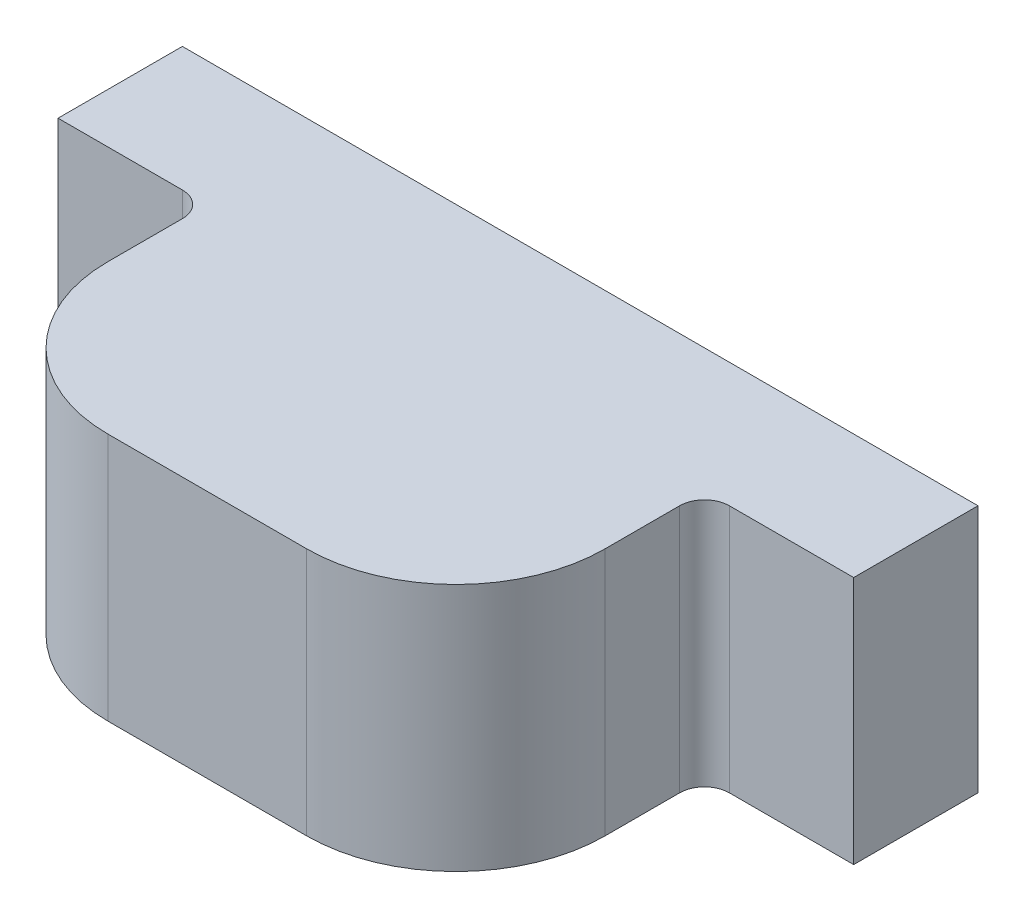
SolidWorks part; units mm, degrees
ref_plane "Front Plane" through (0, 0, 0) normal (0, 0, 1) x (1, 0, 0)
ref_plane "Top Plane" through (0, 0, 0) normal (0, 1, 0) x (1, 0, 0)
ref_plane "Right Plane" through (0, 0, 0) normal (1, 0, 0) x (0, 0, -1)
sketch "Sketch1" plane through (0, 0, 0) normal (0, 1, 0) x (1, 0, 0)
  line L0 (-1.1, -0.25) -> (-1.6, -0.25)
  line L1 (1.6, 0.25) -> (-1.6, 0.25)
  line L2 (1.6, 0.25) -> (1.6, -0.25)
  line L3 (1.6, -0.25) -> (1.1, -0.25)
  line L4 (-1.6, 0.25) -> (-1.6, -0.25)
  line L5 (1.6, 0.25) -> (-1.6, -0.25) construction
  line L6 (1.6, -0.25) -> (-1.6, 0.25) construction
  line L7 (0.4, -1.25) -> (-0.4, -1.25)
  line L8 (1, -0.65) -> (1, -0.35)
  line L10 (-1, -0.65) -> (-1, -0.35)
  line L11 (1, -1.25) -> (-1, -0.25) construction
  line L12 (1, -0.25) -> (-1, -1.25) construction
  arc A0 (0.4, -1.25) -> (1, -0.65) centre (0.4, -0.65) ccw
  arc A1 (-0.4, -1.25) -> (-1, -0.65) centre (-0.4, -0.65) cw
  arc A2 (1, -0.35) -> (1.1, -0.25) centre (1.1, -0.35) cw
  arc A3 (-1.1, -0.25) -> (-1, -0.35) centre (-1.1, -0.35) cw
  point P0 (0, 0)
  point P6 (0, -0.75)
  dimension "D4" = 0.6
  dimension "D5" = 0.1
  dimension "D1" = 2
  dimension "D2" = 1.5
  dimension "D3" = 0.5
  dimension "D6" = 3.2
extrude "Boss-Extrude1" add sketch "Sketch1" along normal blind 1
